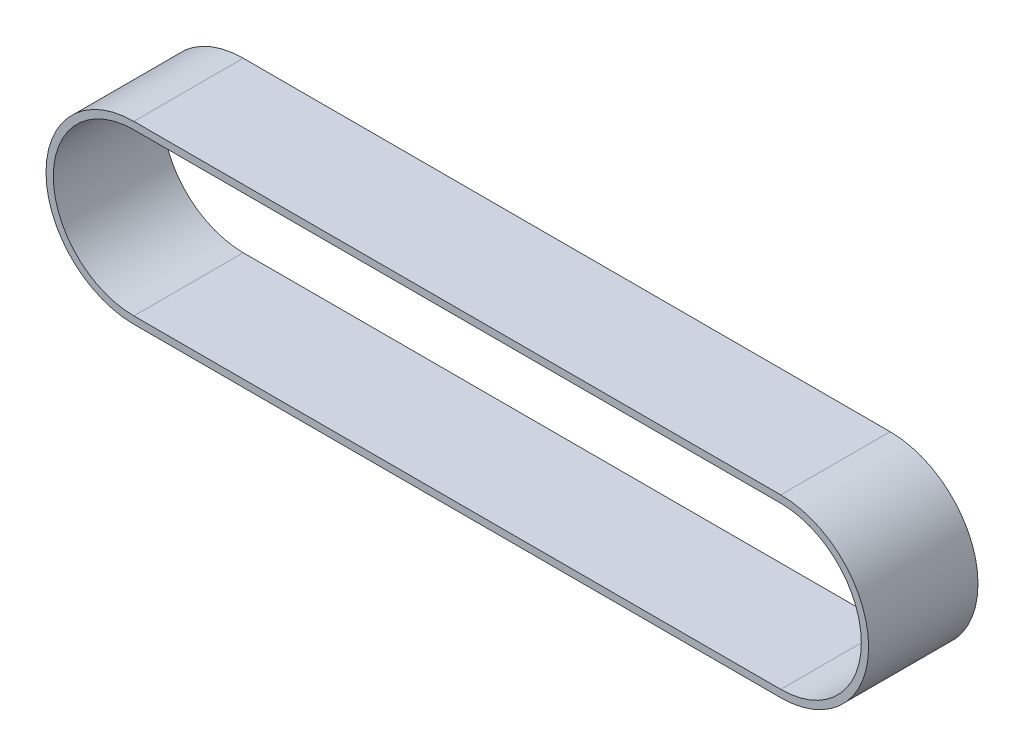
SolidWorks part; units mm, degrees
ref_plane "前视基准面" through (0, 0, 0) normal (0, 0, 1) x (1, 0, 0)
ref_plane "上视基准面" through (0, 0, 0) normal (0, 1, 0) x (1, 0, 0)
ref_plane "右视基准面" through (0, 0, 0) normal (1, 0, 0) x (0, 0, -1)
sketch "草图1" plane through (0, 0, 0) normal (0, 0, 1) x (1, 0, 0)
  line L0 (-61.9916, 0) -> (93.3189, 0) construction
  line L1 (0, 59.0789) -> (0, -43.8536) construction
  line L2 (-44.35, 12.05) -> (44.35, 12.05)
  line L3 (-44.35, 11.05) -> (44.35, 11.05)
  line L4 (44.35, -11.05) -> (-44.35, -11.05)
  line L5 (-44.35, -12.05) -> (44.35, -12.05)
  arc A0 (-44.35, 11.05) -> (-44.35, -11.05) centre (-44.35, 0) ccw
  arc A1 (-44.35, 12.05) -> (-44.35, -12.05) centre (-44.35, 0) ccw
  arc A2 (44.35, 12.05) -> (44.35, -12.05) centre (44.35, 0) cw
  arc A3 (44.35, 11.05) -> (44.35, -11.05) centre (44.35, 0) cw
  dimension "D1" = 22.1
  dimension "D2" = 1
  dimension "D3" = 88.7
extrude "凸台-拉伸1" add sketch "草图1" along normal blind 15
